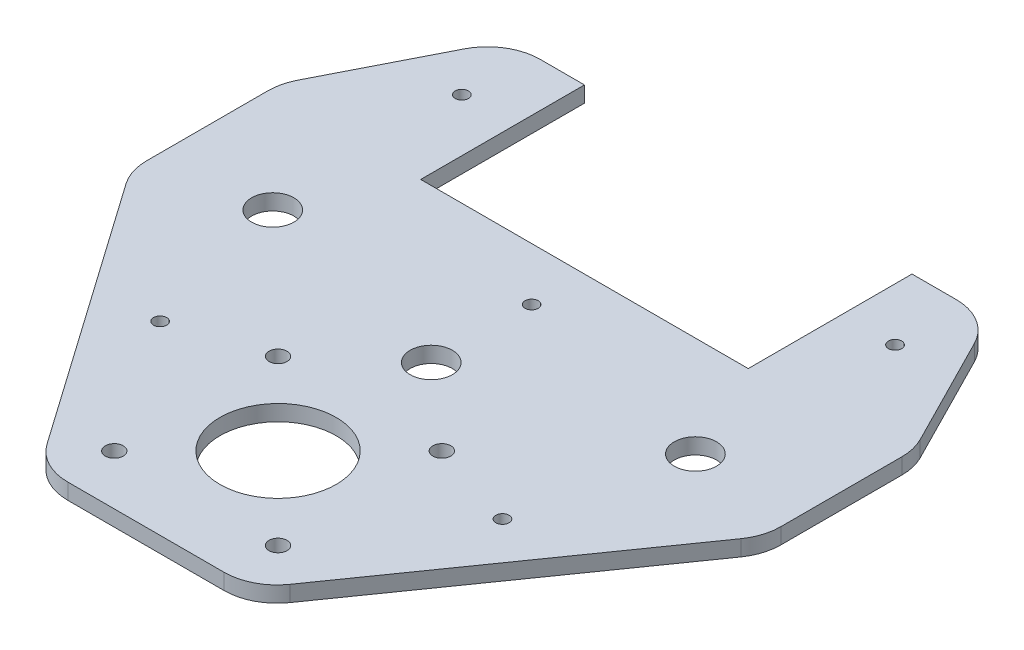
SolidWorks part; units mm, degrees
ref_plane "Front Plane" through (0, 0, 0) normal (0, 0, 1) x (1, 0, 0)
ref_plane "Top Plane" through (0, 0, 0) normal (0, 1, 0) x (1, 0, 0)
ref_plane "Right Plane" through (0, 0, 0) normal (1, 0, 0) x (0, 0, -1)
sketch "Sketch1" plane through (0, 0, 0) normal (0, 1, 0) x (1, 0, 0)
  line L0 (20, -64) -> (-20, -64)
  line L1 (-60, 21.5) -> (-45.5, 50)
  line L2 (60, -7) -> (60, 21.5)
  line L3 (-31, 50) -> (-31, 19)
  line L4 (-60, -7) -> (-60, 21.5)
  line L5 (-31, 50) -> (-45.5, 50)
  line L6 (45.5, 50) -> (31, 50)
  line L8 (45.5, 50) -> (60, 21.5)
  line L9 (31, 19) -> (-31, 19)
  line L10 (31, 50) -> (31, 19)
  line L11 (-60, -7) -> (-20, -64)
  line L12 (20, -64) -> (60, -7)
  circle A0 centre (0, -10) radius 4
  circle A1 centre (-40, 0) radius 4
  circle A2 centre (40, 0) radius 4
  circle A3 centre (-15.5, -23.5) radius 1.7
  circle A4 centre (15.5, -23.5) radius 1.7
  circle A5 centre (15.5, -54.5) radius 1.7
  circle A6 centre (-15.5, -54.5) radius 1.7
  circle A7 centre (0, -39) radius 11
  point P0 (0, 0)
  point P10 (0, -39)
  point P16 (0, -39)
extrude "Boss-Extrude1" add sketch "Sketch1" along normal blind 3
fillet "Fillet1" radius 10 8 edges at (-45.5, 1.5, -50) (-60, 1.5, -21.5) (-60, 1.5, 7) (45.5, 1.5, -50) (60, 1.5, -21.5) (60, 1.5, 7) (-20, 1.5, 64) (20, 1.5, 64)
sketch "Sketch2" plane through (0, 3, 0) normal (0, 1, 0) x (1, 0, 0)
  circle A8 centre (-32.4005, -28.9207) radius 1.25
  circle A9 centre (32.4005, -28.9207) radius 1.25
  circle A10 centre (0, 9) radius 1.25
  circle A11 centre (-41, 36.792) radius 1.25
  circle A12 centre (41, 36.792) radius 1.2556
extrude "Cut-Extrude1" cut sketch "Sketch2" against normal blind 3
